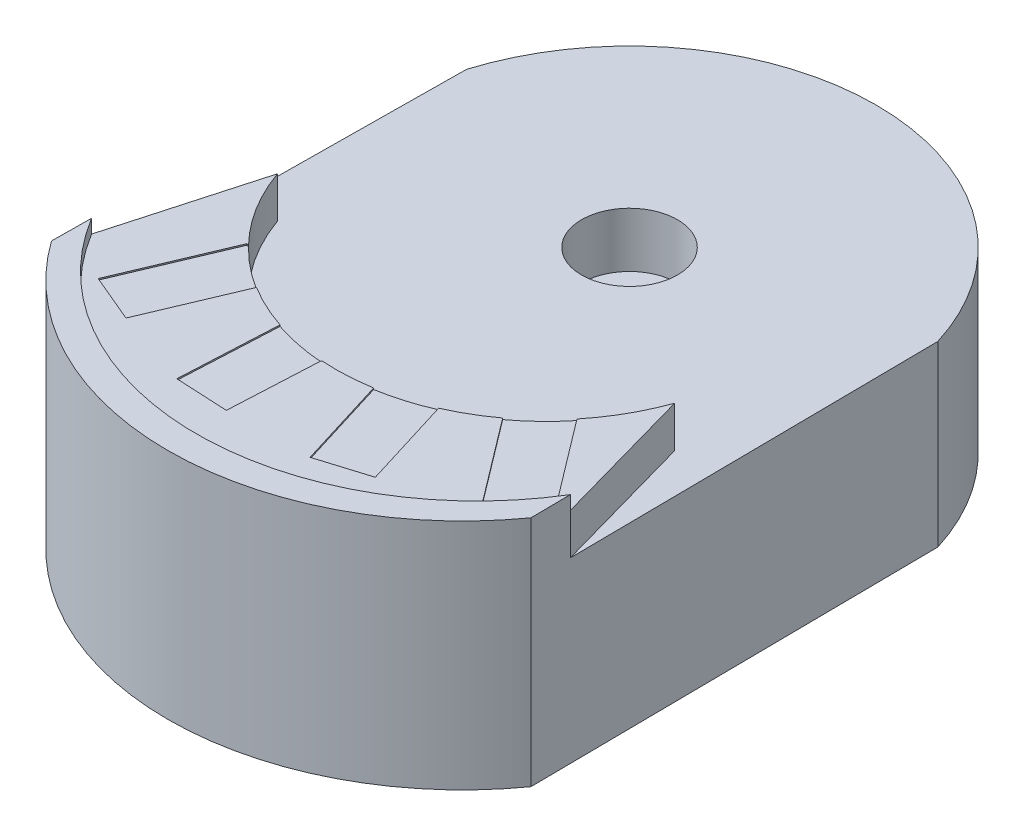
SolidWorks part; units mm, degrees
ref_plane "Front Plane" through (0, 0, 0) normal (0, 0, 1) x (1, 0, 0)
ref_plane "Top Plane" through (0, 0, 0) normal (0, 1, 0) x (1, 0, 0)
ref_plane "Right Plane" through (0, 0, 0) normal (1, 0, 0) x (0, 0, -1)
sketch "Sketch2" plane through (0, 0, 0) normal (0, 1, 0) x (1, 0, 0)
  line L0 (172, 150) -> (-172, 150) construction
  line L1 (-172, 150) -> (-175, -150)
  line L2 (-175, -150) -> (175, -150) construction
  line L3 (175, -150) -> (172, 150)
  line L4 (-211.0388, -240) -> (211.0388, -240) construction
  arc A0 (175, -150) -> (-175, -150) centre (0, -24.8611) cw
  arc A1 (-172, 150) -> (172, 150) centre (0, 96.934) cw
  point P3 (0, 150)
  point P6 (0, -150)
  point P8 (-173.5, 0)
  point P9 (173.5, 0)
  point P14 (0, -240)
  dimension "D4" = 90
  dimension "D5" = 180
  dimension "D1" = 350
  dimension "D2" = 344
  dimension "D3" = 300
extrude "Boss-Extrude1" add sketch "Sketch2" along normal blind 130
sketch "Sketch3" plane through (0, 130, 0) normal (0, 1, 0) x (1, 0, 0)
  line L0 (-175, -150) -> (-174.71, -121)
  line L1 (-172, 150) -> (-175, -150) construction
  line L2 (175, -150) -> (174.71, -121)
  line L3 (175, -150) -> (172, 150) construction
  arc A0 (-175, -150) -> (175, -150) centre (0, -24.8611) ccw construction
  arc A1 (-175, -150) -> (175, -150) centre (0, -24.8611) ccw
  arc A2 (-174.71, -121) -> (174.71, -121) centre (0, -14.3906) ccw
  dimension "D1" = 29
  dimension "D2" = 29
extrude "Boss-Extrude2" add sketch "Sketch3" along normal blind 40
sketch "Sketch4" plane through (0, 130, 0) normal (0, 1, 0) x (1, 0, 0)
  arc A2 (172, 150) -> (-172, 150) centre (0, 96.934) ccw construction
  circle A3 centre (0, 96.934) radius 35
  point P0 (0, 96.934)
  dimension "D1" = 70
extrude "Cut-Extrude1" cut sketch "Sketch4" against normal blind 40
ref_axis "axis the robot arm spins on" through (0, 85.461, -96.934) along (0, 1, 0)
sketch "Sketch5" plane through (0, 130, 0) normal (0, 1, 0) x (1, 0, 0)
  line L0 (-174.71, -121) -> (-145, -15.0882)
  line L1 (174.71, -121) -> (145, -15.0882)
  line L2 (145, -15.0882) -> (-145, -15.0882) construction
  arc A0 (-174.71, -121) -> (174.71, -121) centre (0, -14.3906) ccw construction
  arc A1 (-174.71, -121) -> (174.71, -121) centre (0, -14.3906) ccw
  arc A3 (-145, -15.0882) -> (145, -15.0882) centre (0, 36.4057) ccw
  dimension "D1" = 290
  dimension "D2" = 110
extrude "Boss-Extrude3" add sketch "Sketch5" along normal blind 30
sketch "Sketch6" plane through (0, 160, 0) normal (0, 1, 0) x (1, 0, 0)
  line L0 (0, 96.934) -> (144.2618, -93.6732) construction
  line L1 (-145, -15.0882) -> (-174.71, -121) construction
  line L2 (-145, -15.0882) -> (-174.71, -121) construction
  line L4 (174.71, -121) -> (145, -15.0882) construction
  line L5 (174.71, -121) -> (145, -15.0882)
  line L6 (169.3067, -126.764) -> (119.2169, -60.5824)
  line L8 (169.3067, -126.764) -> (138.927, -149.7571)
  line L9 (138.927, -149.7571) -> (88.8372, -83.5755)
  line L10 (88.8372, -83.5755) -> (119.2169, -60.5824)
  arc A0 (-159.855, -68.0441) -> (159.855, -68.0441) centre (0, 11.656) ccw construction
  arc A1 (-145, -15.0882) -> (145, -15.0882) centre (0, 36.4057) ccw construction
  point P7 (-159.855, -68.0441)
  point P8 (159.855, -68.0441)
  point P18 (144.2618, -93.6732)
  dimension "D1" = 83
  dimension "D2" = 38.1
  dimension "D3" = 30
extrude "Cut-Extrude2" cut sketch "Sketch6" against normal blind 1 contours L10 L6 L8 L9
pattern_circular "CirPattern1" count 4 over 60 about axis through (0, 0, -96.934) along (0, 1, 0) of "Cut-Extrude2"
equation "\"∩╗┐cas_w\" = 38.1mm"
equation "\"cas_l\" = 83.0mm"
equation "\"cas_h\" = 280.0mm"
equation "\"D1@Sketch6\"=\"cas_l\""
equation "\"D2@Sketch6\"=\"∩╗┐cas_w\""
